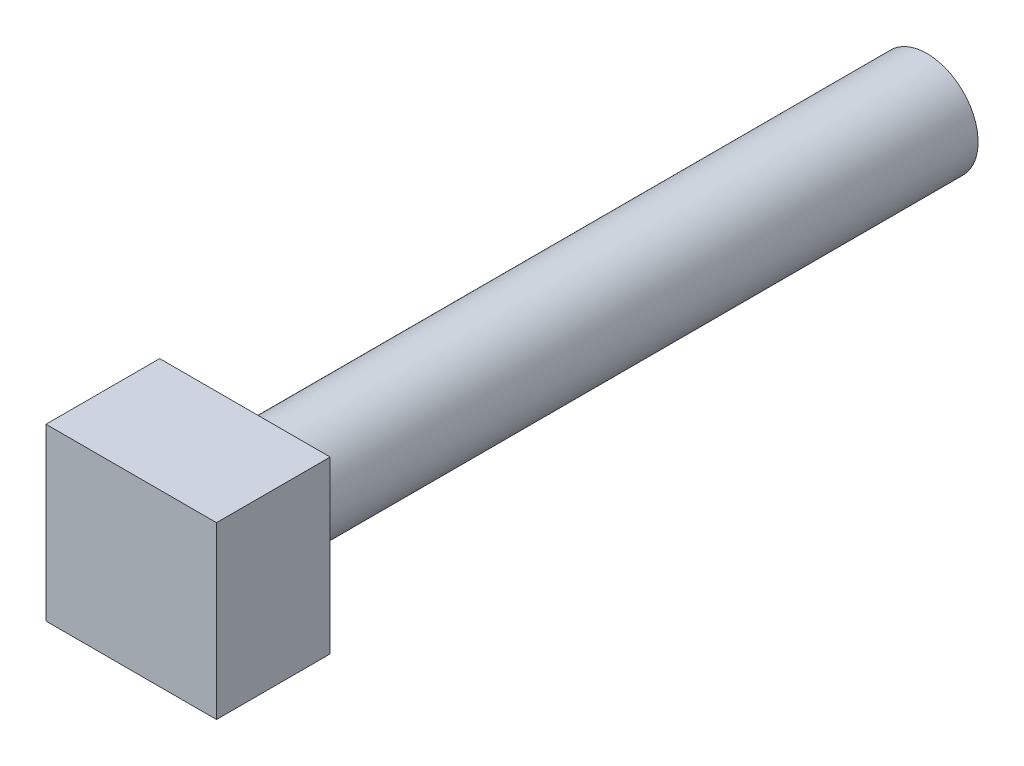
SolidWorks part; units mm, degrees
ref_plane "Front Plane" through (0, 0, 0) normal (0, 0, 1) x (1, 0, 0)
ref_plane "Top Plane" through (0, 0, 0) normal (0, 1, 0) x (1, 0, 0)
ref_plane "Right Plane" through (0, 0, 0) normal (1, 0, 0) x (0, 0, -1)
sketch "Sketch1" plane through (0, 0, 0) normal (0, 0, 1) x (1, 0, 0)
  line L1 (-4.7625, -4.7625) -> (4.7625, -4.7625)
  line L2 (-4.7625, -4.7625) -> (-4.7625, 4.7625)
  line L3 (-4.7625, 4.7625) -> (4.7625, 4.7625)
  line L4 (4.7625, -4.7625) -> (4.7625, 4.7625)
  line L5 (-4.7625, -4.7625) -> (4.7625, 4.7625) construction
  line L6 (-4.7625, 4.7625) -> (4.7625, -4.7625) construction
  point P0 (0, 0)
  dimension "D1" = 9.525
extrude "Boss-Extrude1" add sketch "Sketch1" along normal blind 6.35
sketch "Sketch2" plane through (0, 0, 0) normal (0, 0, -1) x (-1, 0, 0)
  circle A0 centre (0, 0) radius 2.8575
  dimension "D1" = 5.715
extrude "Boss-Extrude2" add sketch "Sketch2" along normal blind 38.1
